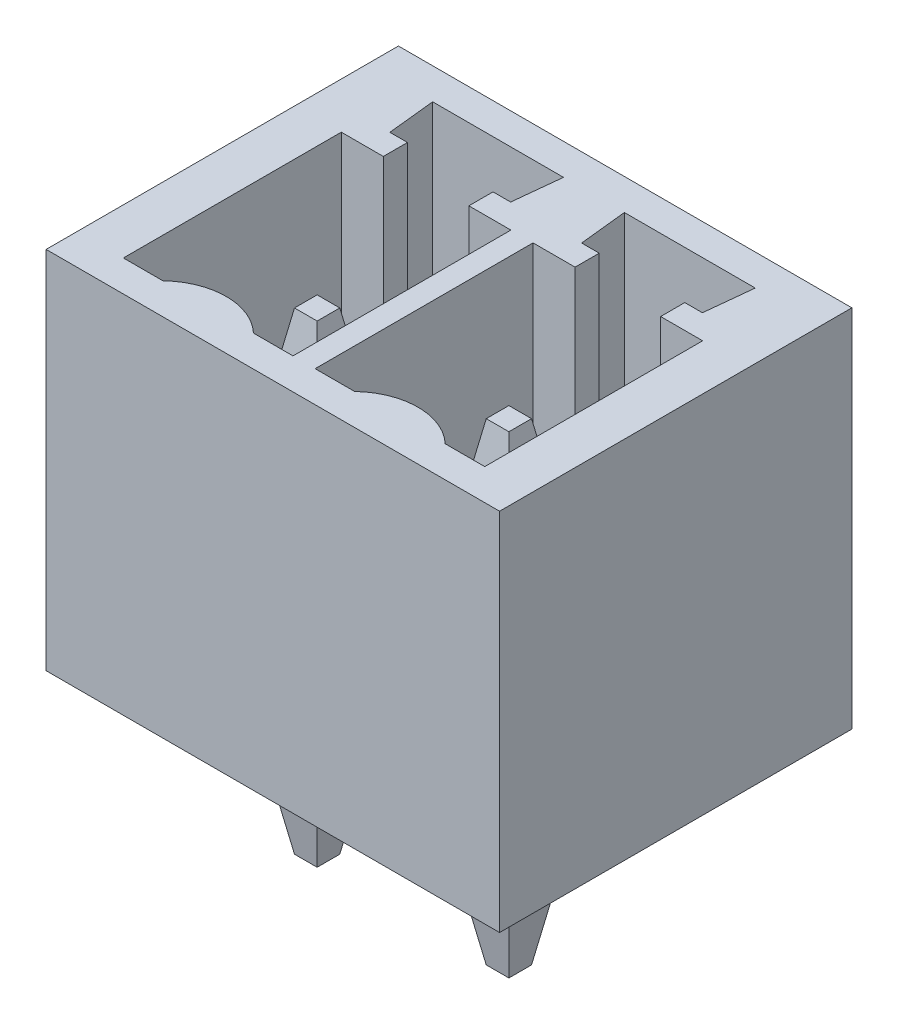
SolidWorks part; units mm, degrees
ref_plane "Front Plane" through (0, 0, 0) normal (0, 0, 1) x (1, 0, 0)
ref_plane "Top Plane" through (0, 0, 0) normal (0, 1, 0) x (1, 0, 0)
ref_plane "Right Plane" through (0, 0, 0) normal (1, 0, 0) x (0, 0, -1)
sketch "Sketch1" plane through (0, 0, 0) normal (0, 1, 0) x (1, 0, 0)
  line L1 (-4.505, -3.5) -> (4.505, -3.5)
  line L2 (-4.505, -3.5) -> (-4.505, 3.5)
  line L3 (-4.505, 3.5) -> (4.505, 3.5)
  line L4 (4.505, -3.5) -> (4.505, 3.5)
  line L5 (-4.505, -3.5) -> (4.505, 3.5) construction
  line L6 (-4.505, 3.5) -> (4.505, -3.5) construction
  point P0 (0, 0)
  dimension "D1" = 7
  dimension "DimB" = 9.01
extrude "Boss-Extrude1" add sketch "Sketch1" along normal blind 7.25
sketch "Sketch2" plane through (0, 7.25, 0) normal (0, 1, 0) x (1, 0, 0)
  line L0 (-3.59, -2.88) -> (-3.59, 1.45)
  line L1 (-3.59, 1.45) -> (-2.755, 1.45)
  line L2 (-2.755, 1.45) -> (-2.755, 1.93)
  line L3 (-2.755, 1.93) -> (-3.105, 1.93)
  line L4 (-3.105, 1.93) -> (-3.205, 2.88)
  line L5 (-3.205, 2.88) -> (-0.605, 2.88)
  line L6 (-1.055, 1.93) -> (-0.705, 1.93)
  line L7 (-1.055, 1.93) -> (-1.055, 1.45)
  line L8 (-1.055, 1.45) -> (-0.22, 1.45)
  line L9 (-0.22, 1.45) -> (-0.22, -2.88)
  line L10 (-3.59, -2.88) -> (-2.805, -2.88)
  line L11 (-0.22, -2.88) -> (-1.005, -2.88)
  line L12 (-1.905, -2.52) -> (-1.905, 2.88) construction
  line L13 (-0.705, 1.93) -> (-0.605, 2.88)
  line L15 (-4.505, 3.5) -> (-4.505, -3.5) construction
  line L16 (-4.505, -3.5) -> (4.505, -3.5) construction
  line L17 (4.505, 3.5) -> (-4.505, 3.5) construction
  line L18 (-3.59, -0.715) -> (-0.22, -0.715) construction
  arc A0 (-2.805, -2.88) -> (-1.005, -2.88) centre (-1.905, -3.825) cw
  point P23 (-1.905, -0.715)
  dimension "D1" = 3.37
  dimension "D2" = 0.48
  dimension "D3" = 1.8
  dimension "D4" = 0.98
  dimension "D5" = 2.6
  dimension "D6" = 0.62
  dimension "D7" = 0.62
  dimension "D8" = 1.7
  dimension "D9" = 2.6
  dimension "D10" = 2.4
  dimension "D11" = 4.33
extrude "Cut-Extrude1" cut sketch "Sketch2" against normal blind 5.45
sketch "Sketch3" plane through (0, 1.8, 0) normal (0, 1, 0) x (1, 0, 0)
  line L1 (-2.33, -0.29) -> (-1.48, -0.29)
  line L2 (-2.33, -0.29) -> (-2.33, -1.14)
  line L3 (-2.33, -1.14) -> (-1.48, -1.14)
  line L4 (-1.48, -0.29) -> (-1.48, -1.14)
  line L5 (-2.33, -0.29) -> (-1.48, -1.14) construction
  line L6 (-2.33, -1.14) -> (-1.48, -0.29) construction
  point P0 (-1.905, -0.715)
  dimension "D2" = 0.85
extrude "Cut-Extrude2" cut sketch "Sketch3" against normal through all
pattern_linear "LPattern1" count 2 spacing 3.81 along (1, 0, 0) of "Cut-Extrude1", "Cut-Extrude2"
sketch "Sketch4" plane through (0, 1.8, 0) normal (0, 1, 0) x (1, 0, 0)
  line L0 (-1.48, -0.29) -> (-2.33, -0.29) construction
  line L1 (-2.33, -0.29) -> (-1.48, -0.29)
  line L2 (-2.33, -0.29) -> (-2.33, -1.14)
  line L3 (-2.33, -1.14) -> (-1.48, -1.14)
  line L4 (-1.48, -0.29) -> (-1.48, -1.14)
  line L5 (-2.33, -1.14) -> (-1.48, -1.14) construction
  line L6 (-2.33, -0.29) -> (-2.33, -1.14) construction
  line L7 (-1.48, -1.14) -> (-1.48, -0.29) construction
extrude "Boss-Extrude2" add sketch "Sketch4" along normal offset from surface 1.1 and the other way blind 5.05 separate body up to face at (1.905, 7.25, -0.58)
chamfer "Chamfer1" distance 0.2 angle 80 8 edges at (-2.33, -3.25, 0.715) (-1.905, -3.25, 0.29) (-1.48, -3.25, 0.715) (-1.905, -3.25, 1.14) (-1.905, 6.15, 0.29) (-1.48, 6.15, 0.715) (-1.905, 6.15, 1.14) (-2.33, 6.15, 0.715)
pattern_linear "LPattern2" count 2 spacing 3.81 along (1, 0, 0) of bodies 105
